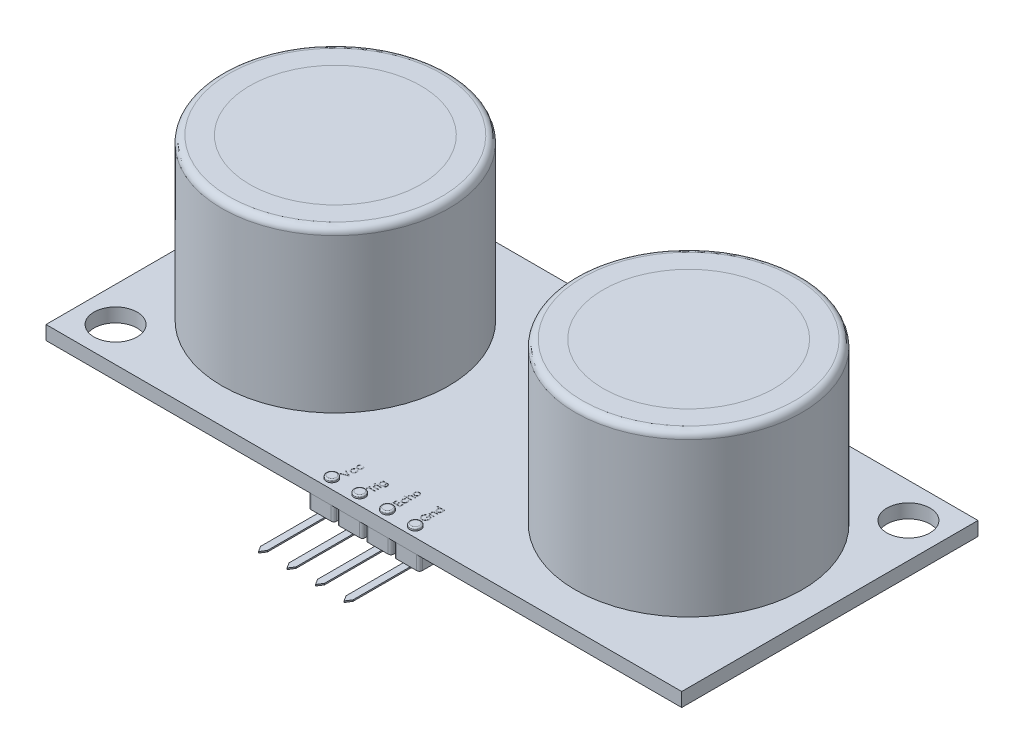
SolidWorks part; units mm, degrees
ref_plane "Front Plane" through (0, 0, 0) normal (0, 0, 1) x (1, 0, 0)
ref_plane "Top Plane" through (0, 0, 0) normal (0, 1, 0) x (1, 0, 0)
ref_plane "Right Plane" through (0, 0, 0) normal (1, 0, 0) x (0, 0, -1)
sketch "Sketch1" plane through (0, 0, 0) normal (0, 1, 0) x (1, 0, 0)
  line L1 (22.85, -10.65) -> (-22.85, -10.65)
  line L2 (22.85, -10.65) -> (22.85, 10.65)
  line L3 (22.85, 10.65) -> (-22.85, 10.65)
  line L4 (-22.85, -10.65) -> (-22.85, 10.65)
  line L5 (22.85, -10.65) -> (-22.85, 10.65) construction
  line L6 (22.85, 10.65) -> (-22.85, -10.65) construction
  circle A0 centre (20.35, 8.15) radius 1.55
  circle A1 centre (-20.35, -8.15) radius 1.55
  point P0 (0, 0)
  dimension "D3" = 3.1
  dimension "D1" = 45.7
  dimension "D2" = 21.3
  dimension "D4" = 2.5
  dimension "D5" = 2.5
  dimension "D6" = 2.5
  dimension "D7" = 2.5
extrude "Boss-Extrude1" add sketch "Sketch1" along normal blind 1
sketch "Sketch2" plane through (0, 1, 0) normal (0, 1, 0) x (1, 0, 0)
  line L0 (0, 0) -> (0, -50000) construction
  circle A0 centre (-12.7, 0) radius 8.15
  circle A1 centre (12.7, 0) radius 8.15
  circle A2 centre (-12.7, 0) radius 6.15
  circle A3 centre (12.7, 0) radius 6.15
  point P4 (20.85, 0)
  point P6 (-20.85, 0)
  dimension "D1" = 16.3
  dimension "D2" = 41.7
  dimension "D3" = 20.85
  dimension "D4" = 2
extrude "Boss-Extrude2" add sketch "Sketch2" along normal blind 11.54 separate body
fillet "Fillet1" radius 0.5 1 edges at (-12.7, 12.54, 8.15)
fillet "Fillet2" radius 0.5 1 edges at (12.7, 12.54, 8.15)
sketch "Sketch3" plane through (0, 1, 0) normal (0, 1, 0) x (1, 0, 0)
  circle A0 centre (-12.7, 0) radius 6
  circle A1 centre (12.7, 0) radius 6
  dimension "D1" = 12
extrude "Boss-Extrude3" add sketch "Sketch3" along normal blind 7 separate body
ref_plane "Plane1" through (12.7, 0, 0) normal (1, 0, 0) x (0, 0, -1)
sketch "Sketch5" plane through (12.7, 0, 0) normal (1, 0, 0) x (0, 0, -1)
  line L0 (0, 8) -> (0, -49992) construction
  line L1 (6, 8) -> (-6, 8) construction
  line L2 (0.75, 8.5) -> (0.75, 8.4)
  line L4 (0.75, 8.5) -> (0, 8.5)
  line L5 (4, 8.915) -> (2, 8)
  line L6 (0.75, 8.4) -> (0.95, 8.4)
  line L7 (0, 8.5) -> (0, 8)
  line L8 (0, 8) -> (2, 8)
  line L9 (0.95, 8.4) -> (4, 8.915)
  point P4 (0, 8)
  dimension "D1" = 4
  dimension "D2" = 0.5
  dimension "D3" = 0.75
  dimension "D4" = 0.1
  dimension "D5" = 2
  dimension "D6" = 15
  dimension "D7" = 0.2
revolve "Revolve1" add sketch "Sketch5" angle 360 about L0
pattern_linear "LPattern2" count 2 spacing 25.4 along (-1, 0, 0) of "Revolve1"
sketch "Sketch6" plane through (0, 12.54, 0) normal (0, 1, 0) x (1, 0, 0)
  circle A0 centre (-12.7, 0) radius 6.15
  circle A1 centre (12.7, 0) radius 6.15
  dimension "D1" = 12.3
extrude "Boss-Extrude4" add sketch "Sketch6" against normal blind 0.2 separate body
sketch "Sketch18" plane through (0, 0, 0) normal (0, -1, 0) x (1, 0, 0)
  line L0 (-22.85, 10.65) -> (22.85, 10.65) construction
  line L1 (-3.8, 10.65) -> (-2.35, 10.65)
  line L2 (-4, 10.45) -> (-4, 8.85)
  line L3 (-3.8, 8.65) -> (-2.35, 8.65)
  line L4 (4, 10.45) -> (4, 8.85)
  line L5 (0, 8.65) -> (0, 10.65) construction
  line L6 (-4, 9.65) -> (4, 9.65) construction
  line L7 (0, 0) -> (0, 50000) construction
  line L8 (-2.15, 10.45) -> (-2.15, 8.85)
  line L9 (0.1, 10.45) -> (0.1, 8.85)
  line L10 (-1.95, 10.45) -> (-1.95, 8.85)
  line L11 (-1.75, 10.65) -> (-0.3, 10.65)
  line L12 (-1.75, 8.65) -> (-0.3, 8.65)
  line L13 (-0.1, 8.85) -> (-0.1, 10.45)
  line L14 (0.3, 10.65) -> (1.75, 10.65)
  line L15 (0.3, 8.65) -> (1.75, 8.65)
  line L16 (1.95, 10.45) -> (1.95, 8.85)
  line L17 (2.15, 10.45) -> (2.15, 8.85)
  line L18 (2.35, 10.65) -> (3.8, 10.65)
  line L19 (2.35, 8.65) -> (3.8, 8.65)
  arc A0 (3.8, 8.65) -> (4, 8.85) centre (3.8, 8.85) ccw
  arc A1 (4, 10.45) -> (3.8, 10.65) centre (3.8, 10.45) ccw
  arc A2 (2.15, 8.85) -> (2.35, 8.65) centre (2.35, 8.85) ccw
  arc A3 (2.15, 10.45) -> (2.35, 10.65) centre (2.35, 10.45) cw
  arc A4 (1.95, 8.85) -> (1.75, 8.65) centre (1.75, 8.85) cw
  arc A5 (1.95, 10.45) -> (1.75, 10.65) centre (1.75, 10.45) ccw
  arc A6 (0.1, 8.85) -> (0.3, 8.65) centre (0.3, 8.85) ccw
  arc A7 (0.1, 10.45) -> (0.3, 10.65) centre (0.3, 10.45) cw
  arc A8 (-0.1, 8.85) -> (-0.3, 8.65) centre (-0.3, 8.85) cw
  arc A9 (-0.1, 10.45) -> (-0.3, 10.65) centre (-0.3, 10.45) ccw
  arc A10 (-1.95, 10.45) -> (-1.75, 10.65) centre (-1.75, 10.45) cw
  arc A11 (-1.95, 8.85) -> (-1.75, 8.65) centre (-1.75, 8.85) ccw
  arc A12 (-2.35, 8.65) -> (-2.15, 8.85) centre (-2.35, 8.85) ccw
  arc A13 (-2.15, 10.45) -> (-2.35, 10.65) centre (-2.35, 10.45) ccw
  arc A14 (-4, 8.85) -> (-3.8, 8.65) centre (-3.8, 8.85) ccw
  arc A15 (-4, 10.45) -> (-3.8, 10.65) centre (-3.8, 10.45) cw
  point P24 (4, 10.65)
  point P27 (2.15, 8.65)
  point P30 (2.15, 10.65)
  point P33 (1.95, 8.65)
  point P38 (0.1, 8.65)
  point P41 (0.1, 10.65)
  point P46 (-0.1, 10.65)
  point P49 (-1.95, 10.65)
  point P52 (-1.95, 8.65)
  point P59 (-4, 8.65)
  point P62 (-4, 10.65)
  point P212 (0, 9.65)
extrude "Boss-Extrude10" add sketch "Sketch18" along normal blind 1 separate body
sketch "Sketch13" plane through (0, 1, 0) normal (0, 1, 0) x (1, 0, 0)
  line L0 (-4, -10.65) -> (-4, -8.7338) construction
  line L1 (-22.85, -10.65) -> (22.85, -10.65) construction
  line L2 (-4, -8.7338) -> (4, -8.7338) construction
  line L3 (4, -8.7338) -> (4, -10.65) construction
  line L4 (4, -10.65) -> (-4, -10.65) construction
  line L5 (0, 0) -> (0, -50000) construction
  circle A0 centre (-3, -9.95) radius 0.4
  circle A1 centre (-1, -9.95) radius 0.4
  circle A2 centre (1, -9.95) radius 0.4
  circle A3 centre (3, -9.95) radius 0.4
  point P9 (-4, -9.6919)
extrude "Boss-Extrude8" add sketch "Sketch13" along normal blind 0.2 separate body
fillet "Fillet3" radius 0.1 1 edges at (-3, 1.2, 10.35)
fillet "Fillet4" radius 0.1 1 edges at (-1, 1.2, 10.35)
fillet "Fillet5" radius 0.1 1 edges at (1, 1.2, 10.35)
fillet "Fillet6" radius 0.1 1 edges at (3, 1.2, 10.35)
sketch "Sketch15" plane through (0, 1, 0) normal (0, 1, 0) x (1, 0, 0)
  line L0 (-22.85, -10.65) -> (22.85, -10.65) construction
  line L1 (3.4865, -7.65) -> (-2.4849, -7.65) construction
  line L2 (3.4865, -7.65) -> (3.4865, -10.65) construction
  line L3 (3.4865, -10.65) -> (-2.4849, -10.65) construction
  line L5 (-2.4849, -7.65) -> (-2.4849, -10.65) construction
  line L6 (3.4865, -7.65) -> (-2.4849, -10.65) construction
  line L7 (3.4865, -10.65) -> (-2.4849, -7.65) construction
  text T0 "Vcc  \r\nTrig   \r\nEcho\r\nGnd " font "Century Gothic" height 0.5
  point P0 (0.5008, -9.15)
  dimension "D1" = 3
extrude "Cut-Extrude5" cut sketch "Sketch15" against normal blind 0.01
sketch "Sketch19" plane through (0, -1, 0) normal (0, -1, 0) x (1, 0, 0)
  line L1 (3.325, 9.15) -> (2.825, 9.15)
  line L2 (3.325, 9.15) -> (3.325, 14.75)
  line L3 (3.075, 15.15) -> (2.825, 15.15)
  line L4 (2.825, 9.15) -> (2.825, 14.75)
  line L5 (3.075, 15.15) -> (3.075, 9.15) construction
  line L6 (3.325, 12.15) -> (2.825, 12.15) construction
  line L7 (1.275, 9.15) -> (0.775, 9.15)
  line L8 (1.275, 9.15) -> (1.275, 14.75)
  line L9 (1.025, 15.15) -> (0.775, 15.15)
  line L10 (0.775, 9.15) -> (0.775, 14.75)
  line L11 (1.025, 15.15) -> (1.025, 9.15) construction
  line L12 (1.275, 12.15) -> (0.775, 12.15) construction
  line L13 (-0.775, 9.15) -> (-1.275, 9.15)
  line L14 (-0.775, 9.15) -> (-0.775, 14.75)
  line L15 (-1.025, 15.15) -> (-1.275, 15.15)
  line L16 (-1.275, 9.15) -> (-1.275, 14.75)
  line L17 (-1.025, 15.15) -> (-1.025, 9.15) construction
  line L18 (-0.775, 12.15) -> (-1.275, 12.15) construction
  line L19 (-2.825, 9.15) -> (-3.325, 9.15)
  line L20 (-2.825, 9.15) -> (-2.825, 14.75)
  line L21 (-3.075, 15.15) -> (-3.325, 15.15)
  line L22 (-3.325, 9.15) -> (-3.325, 14.75)
  line L23 (-3.075, 15.15) -> (-3.075, 9.15) construction
  line L24 (-2.825, 12.15) -> (-3.325, 12.15) construction
  line L26 (-1.75, 8.65) -> (-0.3, 8.65) construction
  line L27 (-3.8, 8.65) -> (-2.35, 8.65) construction
  line L29 (-3.075, 15.15) -> (-2.825, 14.75)
  line L30 (-3.075, 15.15) -> (-3.325, 14.75)
  line L31 (-1.025, 15.15) -> (-0.775, 14.75)
  line L32 (1.025, 15.15) -> (1.275, 14.75)
  line L33 (-1.275, 14.75) -> (-1.025, 15.15)
  line L34 (1.025, 15.15) -> (0.775, 14.75)
  line L35 (3.075, 15.15) -> (3.325, 14.75)
  line L37 (2.825, 14.75) -> (3.075, 15.15)
  point P20 (-1.025, 8.65)
  point P23 (-3.075, 8.65)
  point P300 (-1.025, 12.15)
  point P301 (-3.075, 12.15)
  point P352 (1.025, 12.15)
  point P420 (3.075, 12.15)
  dimension "D2" = 6
  dimension "D3" = 0.5
  dimension "D4" = 0.5
  dimension "D5" = 0.5
  dimension "D6" = 0.5
  dimension "D7" = 0.4
  dimension "D8" = 0.4
  dimension "D9" = 0.4717
extrude "Boss-Extrude11" add sketch "Sketch19" along normal blind 0.1 separate body contours L29 L20 L19 L22 L30 | L31 L14 L13 L16 L33 | L32 L8 L7 L10 L34 | L35 L2 L1 L4 L37
sketch "Sketch21" plane through (0, 1, 0) normal (0, 1, 0) x (1, 0, 0)
  line L0 (22.85, 10.65) -> (-22.85, 10.65) construction
  line L1 (3, 6.65) -> (-3, 6.65)
  line L3 (3, 9.65) -> (-3, 9.65)
  arc A0 (-3, 9.65) -> (-3, 6.65) centre (-3, 8.15) ccw
  arc A1 (3, 6.65) -> (3, 9.65) centre (3, 8.15) ccw
  point P14 (-4.5, 8.15)
  point P16 (4.5, 8.15)
  dimension "D1" = 3
  dimension "D2" = 6
  dimension "D3" = 1
extrude "Boss-Extrude13" add sketch "Sketch21" along normal blind 0.5 separate body
sketch "Sketch22" plane through (0, 1.5, 0) normal (0, 1, 0) x (1, 0, 0)
  line L1 (-2.9874, 7.15) -> (3, 7.15)
  line L3 (-3, 9.15) -> (3, 9.15)
  line L4 (-3, 6.65) -> (3, 6.65) construction
  arc A0 (-3, 9.15) -> (-2.9874, 7.15) centre (-3, 8.15) ccw
  arc A1 (3, 7.15) -> (3, 9.15) centre (3, 8.15) ccw
  arc A2 (-3, 9.65) -> (-3, 6.65) centre (-3, 8.15) ccw construction
  arc A3 (3, 6.65) -> (3, 9.65) centre (3, 8.15) ccw construction
  point P2 (4.5, 8.15)
  point P3 (4, 8.15)
  point P4 (-4.5, 8.15)
  point P5 (-4, 8.1437)
  dimension "D1" = 0.5
  dimension "D3" = 1
  dimension "D2" = 2
  dimension "D4" = 0.5
  dimension "D5" = 0.5
extrude "Boss-Extrude14" add sketch "Sketch22" along normal blind 1.5
fillet "Fillet7" radius 0.1 8 edges at (-4, 3, -8.1437) (0, 3, -9.15) (4, 3, -8.15) (-4.5, 1.5, -8.15) (0, 1.5, -9.65) (4.5, 1.5, -8.15) (0.0063, 3, -7.15) (0, 1.5, -6.65)
equation "\"D2@Sketch13\"=\"D1@Sketch13\"/2"
equation "\"D9@Sketch18\"=\"D1@Sketch18\"/2"
